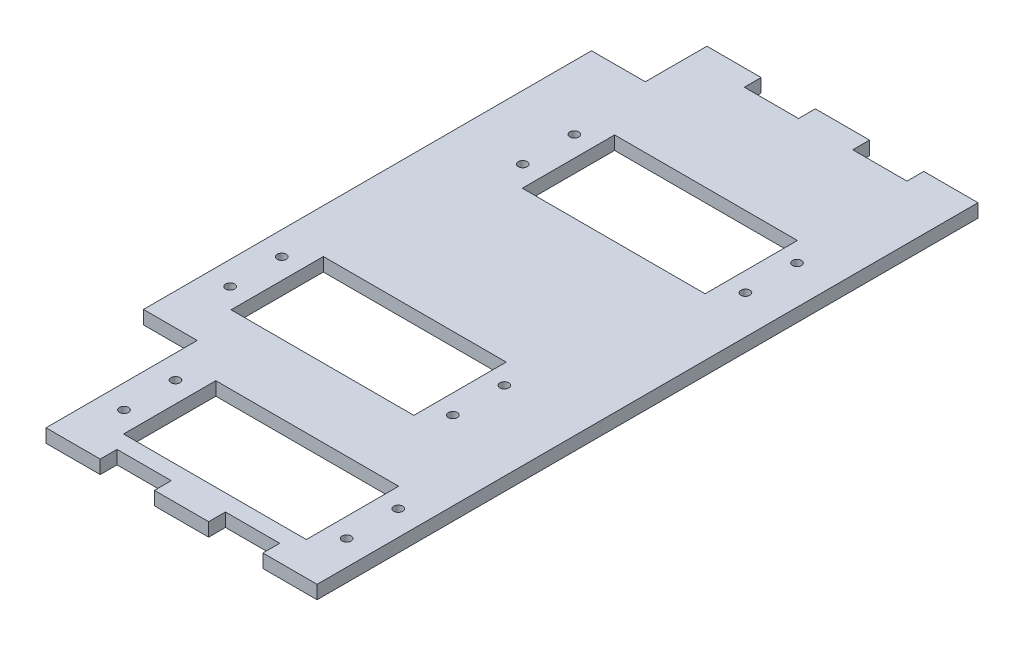
SolidWorks part; units mm, degrees
material "ABS"
ref_plane "Front Plane" through (0, 0, 0) normal (0, 0, 1) x (1, 0, 0)
ref_plane "Top Plane" through (0, 0, 0) normal (0, 1, 0) x (1, 0, 0)
ref_plane "Right Plane" through (0, 0, 0) normal (1, 0, 0) x (0, 0, -1)
sketch "Sketch1" plane through (0, 0, 0) normal (0, 1, 0) x (1, 0, 0)
  line L0 (0, -70) -> (0, -56) construction
  line L1 (-30.25, -70) -> (30.25, -70) construction
  line L2 (-30.25, -70) -> (-30.25, 70) construction
  line L4 (30.25, -70) -> (30.25, 70)
  line L5 (-30.25, -70) -> (30.25, 70) construction
  line L6 (-30.25, 70) -> (30.25, -70) construction
  line L7 (0, -56) -> (0, -20) construction
  line L8 (-20.4, -45.7) -> (20.4, -45.7)
  line L9 (-20.4, -45.7) -> (-20.4, -66.3)
  line L10 (-20.4, -66.3) -> (20.4, -66.3)
  line L11 (20.4, -45.7) -> (20.4, -66.3)
  line L12 (-20.4, -45.7) -> (20.4, -66.3) construction
  line L13 (-20.4, -66.3) -> (20.4, -45.7) construction
  line L14 (0, -20) -> (0, 36) construction
  line L15 (-20.4, -9.7) -> (20.4, -9.7) construction
  line L16 (-20.4, -9.7) -> (-20.4, -30.3) construction
  line L17 (-20.4, -30.3) -> (20.4, -30.3) construction
  line L18 (20.4, -9.7) -> (20.4, -30.3) construction
  line L19 (-20.4, -9.7) -> (20.4, -30.3) construction
  line L20 (-20.4, -30.3) -> (20.4, -9.7) construction
  line L21 (-30.25, -70) -> (30.25, -70) construction
  line L22 (-20.4, 25.7) -> (20.4, 25.7) construction
  line L23 (-20.4, 25.7) -> (-20.4, 46.3) construction
  line L24 (-20.4, 46.3) -> (20.4, 46.3) construction
  line L25 (20.4, 25.7) -> (20.4, 46.3) construction
  line L26 (-20.4, 25.7) -> (20.4, 46.3) construction
  line L27 (-20.4, 46.3) -> (20.4, 25.7) construction
  line L28 (-30.25, -70) -> (-30.25, -73.75)
  line L29 (30.25, -70) -> (30.25, -73.75)
  line L31 (30.25, -71.875) -> (18.15, -71.875) construction
  line L32 (18.15, -70) -> (18.15, -73.75)
  line L33 (30.25, -73.75) -> (18.15, -73.75)
  line L34 (30.25, -73.75) -> (30.25, -70)
  line L35 (6.05, -70) -> (18.15, -70)
  line L36 (18.15, -73.75) -> (6.05, -73.75) construction
  line L37 (6.05, -73.75) -> (6.05, -70)
  line L38 (6.05, -73.75) -> (-6.05, -73.75)
  line L39 (-6.05, -73.75) -> (-18.15, -73.75) construction
  line L40 (-18.15, -73.75) -> (-30.25, -73.75)
  line L41 (-6.05, -73.75) -> (-6.05, -70)
  line L42 (-18.15, -73.75) -> (-18.15, -70)
  line L43 (-6.05, -70) -> (-18.15, -70)
  line L44 (30.25, 0) -> (-30.25, 0) construction
  line L45 (-6.05, 70) -> (-18.15, 70)
  line L46 (6.05, 70) -> (18.15, 70)
  line L47 (-18.15, 73.75) -> (-30.25, 73.75)
  line L48 (-6.05, 73.75) -> (-18.15, 73.75) construction
  line L49 (18.15, 73.75) -> (6.05, 73.75) construction
  line L50 (30.25, 71.875) -> (18.15, 71.875) construction
  line L51 (-18.15, 73.75) -> (-18.15, 70)
  line L52 (-6.05, 73.75) -> (-6.05, 70)
  line L53 (6.05, 73.75) -> (-6.05, 73.75)
  line L54 (6.05, 73.75) -> (6.05, 70)
  line L55 (30.25, 73.75) -> (30.25, 70)
  line L56 (30.25, 73.75) -> (18.15, 73.75)
  line L57 (18.15, 70) -> (18.15, 73.75)
  line L58 (30.25, 70) -> (30.25, 73.75)
  line L59 (-30.25, 70) -> (-30.25, 73.75)
  line L60 (-30.25, -70) -> (-30.25, -40)
  line L61 (-30.25, -40) -> (-42.25, -40)
  line L62 (-42.25, -40) -> (-42.25, 60)
  line L63 (-42.25, 60) -> (-30.25, 60)
  line L64 (-30.25, 60) -> (-30.25, 70)
  line L65 (0, -20) -> (-12, -20) construction
  line L66 (0, 36) -> (-3, 36) construction
  line L67 (8.4, -9.7) -> (-32.4, -9.7)
  line L68 (8.4, -9.7) -> (8.4, -30.3)
  line L69 (8.4, -30.3) -> (-32.4, -30.3)
  line L70 (-32.4, -9.7) -> (-32.4, -30.3)
  line L71 (8.4, -9.7) -> (-32.4, -30.3) construction
  line L72 (8.4, -30.3) -> (-32.4, -9.7) construction
  line L74 (17.4, 46.3) -> (-23.4, 46.3)
  line L75 (17.4, 46.3) -> (17.4, 25.7)
  line L76 (17.4, 25.7) -> (-23.4, 25.7)
  line L77 (-23.4, 46.3) -> (-23.4, 25.7)
  line L78 (17.4, 46.3) -> (-23.4, 25.7) construction
  line L79 (17.4, 25.7) -> (-23.4, 46.3) construction
  circle A0 centre (-25.6879, -6.6503) radius 1.8167 construction
  point P0 (0, 0)
  point P29 (18.15, -71.875)
  dimension "D1" = 140
  dimension "D2" = 60.5
  dimension "D3" = 14
  dimension "D4" = 40.8
  dimension "D5" = 20.6
  dimension "D6" = 36
  dimension "D7" = 20.6
  dimension "D8" = 40.8
  dimension "D9" = 56
  dimension "D10" = 20.6
  dimension "D11" = 40.8
  dimension "D12" = 3.75
  dimension "D13" = 12.1
  dimension "D14" = 12.1
  dimension "D15" = 12.1
  dimension "D16" = 12.1
  dimension "D17" = 12
  dimension "D18" = 100
  dimension "D19" = 30
  dimension "D20" = 12
  dimension "D21" = 40.8
  dimension "D22" = 20.6
  dimension "D23" = 3
  dimension "D24" = 20.6
  dimension "D25" = 40.8
extrude "Boss-Extrude4" add sketch "Sketch1" along normal blind 3
sketch "Sketch2" plane through (0, 3, 0) normal (0, 1, 0) x (1, 0, 0)
  line L0 (30.25, 73.75) -> (30.25, -73.75) construction
  circle A0 centre (-25, -50.1) radius 1
  circle A1 centre (-25, -61.6) radius 1
  circle A2 centre (-37, -25.9) radius 1
  circle A3 centre (-28, 30.4) radius 1
  circle A4 centre (-28, 41.9) radius 1
  circle A5 centre (21.7, 41.9) radius 1
  circle A6 centre (21.7, 30.4) radius 1
  circle A7 centre (12.7, -14.4) radius 1
  circle A8 centre (12.7, -25.9) radius 1
  circle A9 centre (24.7, -50.1) radius 1
  circle A10 centre (24.7, -61.6) radius 1
  circle A11 centre (-37, -14.4) radius 1
  dimension "D1" = 2
  dimension "D2" = 2
  dimension "D3" = 2
  dimension "D4" = 2
  dimension "D5" = 2
  dimension "D6" = 2
  dimension "D7" = 2
  dimension "D8" = 2
  dimension "D9" = 2
  dimension "D10" = 2
  dimension "D11" = 2
  dimension "D12" = 2
  dimension "D13" = 17.55
  dimension "D14" = 17.55
  dimension "D15" = 67.25
  dimension "D16" = 67.25
  dimension "D17" = 5.55
  dimension "D18" = 5.55
  dimension "D19" = 55.25
  dimension "D20" = 55.25
  dimension "D21" = 8.55
  dimension "D22" = 8.55
  dimension "D23" = 58.25
  dimension "D24" = 58.25
extrude "Cut-Extrude1" cut sketch "Sketch2" against normal through all
equation "\"MotorLength\" = 40.5mm"
equation "\"MotorWidth\" = 20.3mm"
equation "\"AttachmentHeight\"= 3mm"
equation "\"SpoolDiameter\"= 60mm"
equation "\"SpoolHeight\"= 2mm"
equation "\"SpoolRidgeHeight\"= 1mm"
equation "\"SpoolRidgeDepth\"= 2mm"
equation "\"OuterThickness\"= 3mm"
equation "\"MasterFillet\"= 3mm"
equation "\"PartSeperation\"= 6mm"
equation "\"Tolerance\"= 0.15mm"
equation "\"HeightPart\"= 100mm"
equation "\"Holes\"= 1.5mm"
equation "\"SpineHolderThickness\"= 3mm"
equation "\"SpineHolderDepth\" = 3mm"
equation "\"SpoolSeperation\"= 2mm"
equation "\"D1@Sketch1\"=3*((\"SpoolDiameter\"/3)*2+\"SpoolRidgeDepth\"*2+\"SpoolSeperation\")+\"SpoolSeperation\""
equation "\"D2@Sketch1\"=\"MotorLength\"+\"ServoHolderWidthOffset\""
equation "\"D3@Sketch1\"=\"SpoolSeperation\"+( \"SpoolRidgeDepth\")+\"SpoolDiameter\"/(2*3)"
equation "\"D4@Sketch1\"=\"MotorLength\"+\"Tolerance\"*2"
equation "\"D5@Sketch1\"=\"MotorWidth\"+\"Tolerance\"*2"
equation "\"D6@Sketch1\"=(\"SpoolDiameter\")/(3*2)+(\"SpoolDiameter\"/3)+\"SpoolSeperation\"+\"SpoolRidgeDepth\"*2"
equation "\"D7@Sketch1\"=\"MotorWidth\"+\"Tolerance\"*2"
equation "\"D8@Sketch1\"=\"MotorLength\"+\"Tolerance\"*2"
equation "\"D9@Sketch1\"=\"SpoolDiameter\"/2+\"SpoolDiameter\"/3+\"SpoolSeperation\"+\"SpoolRidgeDepth\"*2"
equation "\"D10@Sketch1\"=\"MotorWidth\"+\"Tolerance\"*2"
equation "\"D11@Sketch1\"=\"MotorLength\"+\"Tolerance\"*2"
equation "\"D12@Sketch1\"=\"SpineHolderDepth\"*1.25"
equation "\"D13@Sketch1\"=(\"MotorLength\"+\"ServoHolderWidthOffset\")*1/5"
equation "\"D14@Sketch1\"=(\"MotorLength\"+\"ServoHolderWidthOffset\")*1/5"
equation "\"D15@Sketch1\"=(\"MotorLength\"+\"ServoHolderWidthOffset\")*1/5"
equation "\"D16@Sketch1\"=(\"MotorLength\"+\"ServoHolderWidthOffset\")*1/5"
equation "\"ServoHolderWidthOffset\"= 20mm"
equation "\"ServoFastenerHolders\"=2mm"
equation "\"D1@Sketch2\"=\"ServoFastenerHolders\""
equation "\"D2@Sketch2\"=\"ServoFastenerHolders\""
equation "\"D3@Sketch2\"=\"ServoFastenerHolders\""
equation "\"D4@Sketch2\"=\"ServoFastenerHolders\""
equation "\"D5@Sketch2\"=\"ServoFastenerHolders\""
equation "\"D6@Sketch2\"=\"ServoFastenerHolders\""
equation "\"D7@Sketch2\"=\"ServoFastenerHolders\""
equation "\"D8@Sketch2\"=\"ServoFastenerHolders\""
equation "\"D9@Sketch2\"=\"ServoFastenerHolders\""
equation "\"D11@Sketch2\"=\"ServoFastenerHolders\""
equation "\"D12@Sketch2\"=\"ServoFastenerHolders\""
equation "\"MotorTransmitterToScrew\"= 21.7mm"
equation "\"SpoolToSpine\"= 15mm"
equation "\"SpoolCenterToMotor\" = 31.5mm"
equation "\"HubOffset\"= 18mm"
equation "\"MiddleServoOffset\"= 12mm"
equation "\"LargeServoOffset\"= 3mm"
equation "\"SmallServoOffset\"= 0mm"
equation "\"D20@Sketch1\"=\"MiddleServoOffset\""
equation "\"D13@Sketch2\"=\"MiddleServoOffset\"+5.55"
equation "\"D14@Sketch2\"=\"MiddleServoOffset\"+5.55"
equation "\"D15@Sketch2\"=\"MiddleServoOffset\"+55.25"
equation "\"D16@Sketch2\"=\"MiddleServoOffset\"+55.25"
equation "\"D17@Sketch2\"=\"SmallServoOffset\"+5.55"
equation "\"D18@Sketch2\"=\"SmallServoOffset\"+5.55"
equation "\"D19@Sketch2\"=\"SmallServoOffset\"+55.25"
equation "\"D20@Sketch2\"=\"SmallServoOffset\"+55.25"
equation "\"D21@Sketch2\"=\"LargeServoOffset\"+5.55"
equation "\"D22@Sketch2\"=\"LargeServoOffset\"+5.55"
equation "\"D23@Sketch2\"=\"LargeServoOffset\"+55.25"
equation "\"D24@Sketch2\"=\"LargeServoOffset\"+55.25"
equation "\"D23@Sketch1\"=\"LargeServoOffset\""
equation "\"D24@Sketch1\"=\"MotorWidth\"+\"Tolerance\"*2"
equation "\"D25@Sketch1\"=\"MotorLength\"+\"Tolerance\"*2"
equation "\"D17@Sketch1\"=\"MiddleServoOffset\""
equation "\"D10@Sketch2\"=\"ServoFastenerHolders\""
equation "\"DiscThickness\"= 4mm"
equation "\"LigamentThickness\"= 2mm"
equation "\"LigamentExtension\"= 1mm"
equation "\"LigamentAngle\"= 20deg"
equation "\"SpineDiameter\"= 15mm"
equation "\"LigamentDepth\"= 1mm"
equation "\"ArduinoLength\" = 53.4mm"
equation "\"ArduinoWidth\" = 50mm"
equation "\"ArdYOffset\" = 29.5mm"
equation "\"ArdXOffset\" = 20.5mm"
equation "\"ArdXOffsetSmall\" = 25mm"
equation "\"ToolHoleDiameter\"= 12mm"
